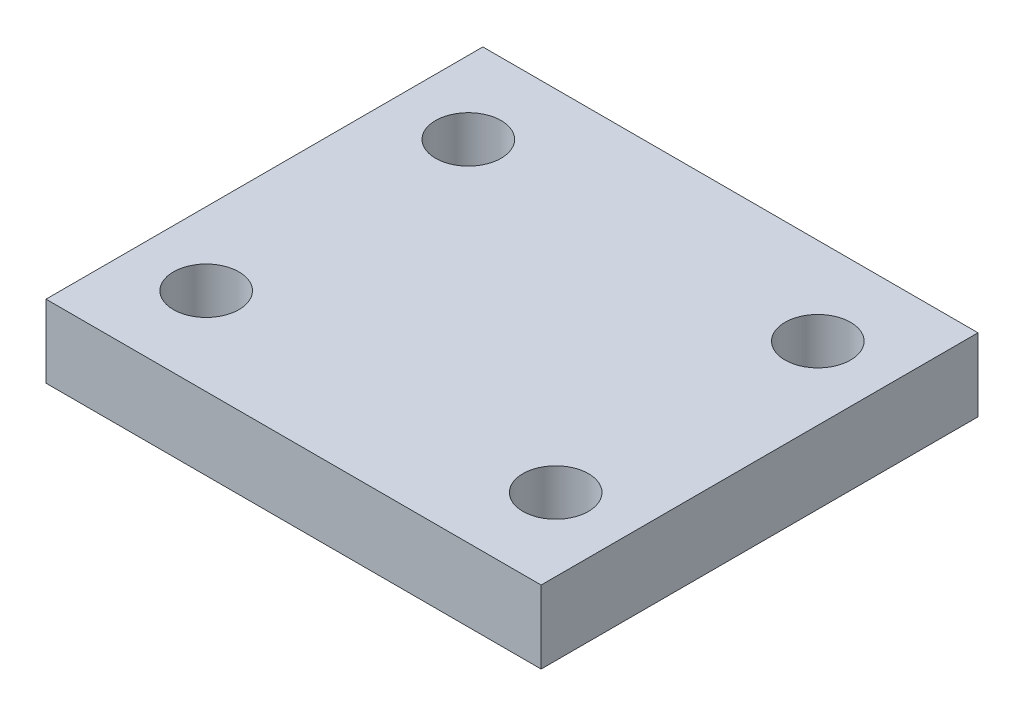
SolidWorks part; units mm, degrees
material "Balsa"
ref_plane "Front Plane" through (0, 0, 0) normal (0, 0, 1) x (1, 0, 0)
ref_plane "Top Plane" through (0, 0, 0) normal (0, 1, 0) x (1, 0, 0)
ref_plane "Right Plane" through (0, 0, 0) normal (1, 0, 0) x (0, 0, -1)
sketch "Sketch1" plane through (0, 0, 0) normal (0, 1, 0) x (1, 0, 0)
  line L1 (0, 0) -> (34, 0)
  line L2 (0, 0) -> (0, 30)
  line L3 (0, 30) -> (34, 30)
  line L4 (34, 0) -> (34, 30)
  circle A0 centre (5, 6) radius 2.25
  circle A1 centre (29, 6) radius 2.25
  circle A2 centre (29, 24) radius 2.25
  circle A3 centre (5, 24) radius 2.25
  dimension "D3" = 4.5
  dimension "D4" = 6
  dimension "D6" = 5
  dimension "D7" = 5
  dimension "D1" = 30
  dimension "D2" = 34
  dimension "D5" = 6
extrude "Boss-Extrude1" add sketch "Sketch1" along normal blind 5
